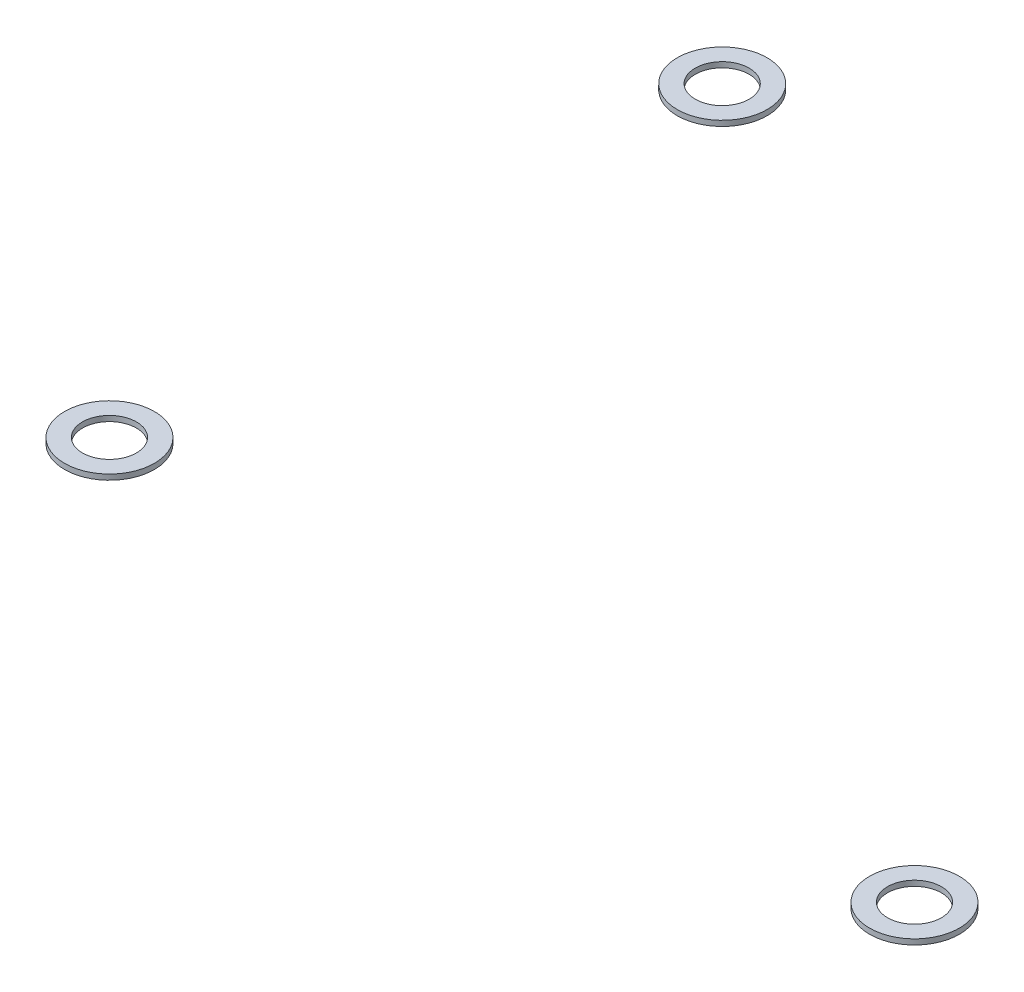
SolidWorks part; units mm, degrees
ref_plane "Front Plane" through (0, 0, 0) normal (0, 0, 1) x (1, 0, 0)
ref_plane "Top Plane" through (0, 0, 0) normal (0, 1, 0) x (1, 0, 0)
ref_plane "Right Plane" through (0, 0, 0) normal (1, 0, 0) x (0, 0, -1)
sketch "Sketch1" plane through (0, 0, 0) normal (0, 1, 0) x (1, 0, 0)
  line L0 (-22.4, 17.05) -> (-22.4, -17.05) construction
  line L1 (-22.4, -17.05) -> (22.4, -17.05) construction
  line L2 (22.4, -17.05) -> (-22.4, 17.05) construction
  circle A0 centre (-22.4, 17.05) radius 1.5
  circle A1 centre (-22.4, -17.05) radius 1.5
  circle A2 centre (22.4, -17.05) radius 1.5
  circle A3 centre (-22.4, 17.05) radius 2.5
  circle A4 centre (-22.4, -17.05) radius 2.5
  circle A5 centre (22.4, -17.05) radius 2.5
  dimension "D1" = 3
  dimension "D2" = 5
  dimension "D3" = 34.1
  dimension "D4" = 44.8
extrude "Boss-Extrude1" add sketch "Sketch1" along normal blind 0.3
